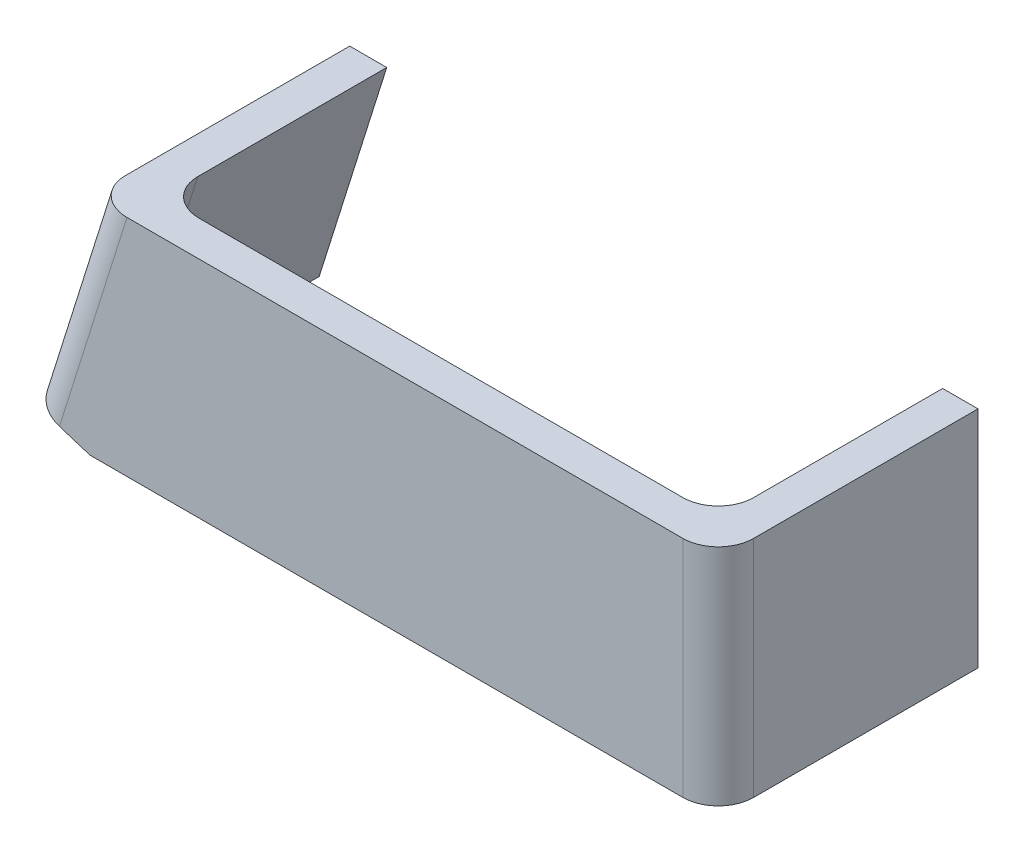
SolidWorks part; units mm, degrees
material "PE High Density"
ref_plane "Front Plane" through (0, 0, 0) normal (0, 0, 1) x (1, 0, 0)
ref_plane "Top Plane" through (0, 0, 0) normal (0, 1, 0) x (1, 0, 0)
ref_plane "Right Plane" through (0, 0, 0) normal (1, 0, 0) x (0, 0, -1)
sketch "Sketch1" plane through (0, 0, 0) normal (0, 0, 1) x (1, 0, 0)
  line L1 (-44.433, 15.875) -> (44.467, 15.875)
  line L3 (-44.433, -15.875) -> (44.467, -15.875)
  line L10 (-44.433, 15.875) -> (-53.5192, -13.0175)
  line L12 (0.017, -15.875) -> (0.017, 75.0464) construction
  line L13 (0.017, -15.875) -> (147.1451, -15.875) construction
  line L15 (44.467, 15.875) -> (44.467, -15.875)
  line L17 (-44.433, -15.875) -> (-53.5192, -13.0175)
extrude "Boss-Extrude1" add sketch "Sketch1" along normal blind 5
sketch "Sketch2" plane through (0, 0, 0) normal (0, 0, -1) x (-1, 0, 0)
  line L0 (-39.467, 15.875) -> (-39.467, -15.875)
  line L1 (-44.467, 15.875) -> (44.433, 15.875) construction
  line L2 (44.433, -15.875) -> (-44.467, -15.875) construction
  line L3 (48.7495, -14.5175) -> (39.1915, 15.875)
  line L4 (53.5192, -13.0175) -> (44.433, -15.875) construction
  line L5 (-44.467, -15.875) -> (-44.467, 15.875) construction
  line L6 (44.433, 15.875) -> (53.5192, -13.0175) construction
  line L7 (-39.467, -15.875) -> (-44.467, -15.875)
  line L8 (-44.467, -15.875) -> (-44.467, 15.875)
  line L9 (-44.467, 15.875) -> (-39.467, 15.875)
  line L10 (48.7495, -14.5175) -> (53.5192, -13.0175)
  line L11 (53.5192, -13.0175) -> (44.433, 15.875)
  line L12 (44.433, 15.875) -> (39.1915, 15.875)
  dimension "D1" = 5
  dimension "D2" = 5
extrude "Boss-Extrude2" add sketch "Sketch2" along normal blind 31.75
fillet "Fillet1" radius 5 4 edges at (-48.9761, 1.4287, 5) (-43.9705, 0.6787, 0) (39.467, 0, 0) (44.467, 0, 5)
equation "\"Plate Screw Hole Diameter\"= 0.116in"
equation "\"Plate Width\" = 3.5in"
equation "\"Plate Thickness\" = 0.375in"
equation "\"Num holes\" = 4"
equation "\"Plate Height\" = 1.25in"
equation "\"D1@Sketch11\"=\"Plate Width\" / ( \"Num holes\" + 1)"
equation "\"D2@Sketch11\"=\"Plate Thickness\"/2"
equation "\"D3\" = \"Plate Width\" /  ( \"Num holes\" + 1 ) "
equation "\"Top Plate Width\" = 4.5in"
equation "\"Plate Clearance Hole Diameter\" = 0.125in"
equation "\"Plate Tap Hole Diameter\" = 0.116in"
equation "\"Bottom Plate Length\" = 6.5in"
equation "\"Number Eight Clearance Size\" = 0.177in"
equation "\"back_brace_height_offset\"=0.35"
equation "\"D2@Sketch13\"=\"Plate Tap Hole Diameter\""
